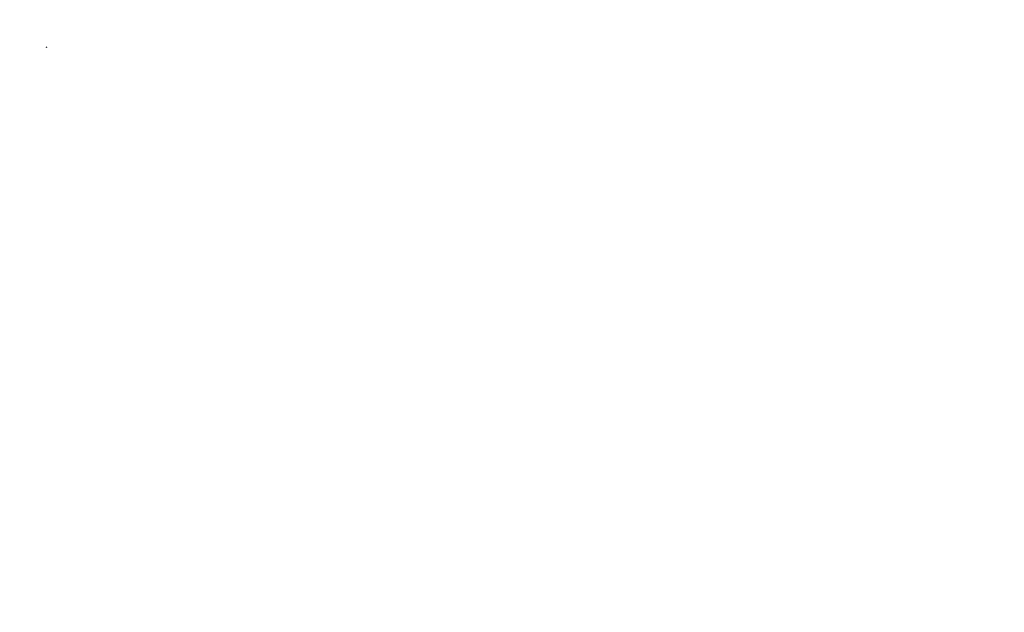
SolidWorks part; units mm, degrees
ref_plane "Front Plane" through (0, 0, 0) normal (0, 0, 1) x (1, 0, 0)
ref_plane "Top Plane" through (0, 0, 0) normal (0, 1, 0) x (1, 0, 0)
ref_plane "Right Plane" through (0, 0, 0) normal (1, 0, 0) x (0, 0, -1)
sketch "Sketch1" plane through (0, 0, 0) normal (0, 1, 0) x (1, 0, 0)
  line L0 (0, 10.9842) -> (0, -10.9842)
  arc A0 (0, -10.9842) -> (0, 10.9842) centre (0, 0) ccw
  dimension "D1" = 21.9685
revolve "Revolve-Sun" add sketch "Sketch1" angle 360 about L0
sketch "Sketch10" plane through (0, 0, 0) normal (0, 1, 0) x (1, 0, 0)
  line L0 (456.9844, 0.0394) -> (456.9844, -0.0394)
  circle A0 centre (0, 0) radius 456.9844 construction
  arc A1 (456.9844, -0.0394) -> (456.9844, 0.0394) centre (456.9844, 0) ccw
  dimension "D1" = 913.9687
  dimension "D2" = 0.0787
revolve "Revolve-Mercury" add sketch "Sketch10" angle 360 about L0
sketch "Sketch9" plane through (0, 0, 0) normal (0, 1, 0) x (1, 0, 0)
  line L0 (853.9235, 0.0955) -> (853.9235, -0.0955)
  circle A0 centre (0, 0) radius 853.9235 construction
  arc A1 (853.9235, -0.0955) -> (853.9235, 0.0955) centre (853.9235, 0) ccw
  dimension "D1" = 1707.847
  dimension "D2" = 0.191
revolve "Revolve-Venus" add sketch "Sketch9" angle 360 about L0
sketch "Sketch7" plane through (0, 0, 0) normal (0, 1, 0) x (1, 0, 0)
  line L0 (1180.5418, 0.1006) -> (1180.5418, -0.1006)
  circle A0 centre (0, 0) radius 1180.5418 construction
  arc A1 (1180.5418, -0.1006) -> (1180.5418, 0.1006) centre (1180.5418, 0) ccw
  dimension "D1" = 2361.0837
  dimension "D2" = 0.2011
revolve "Revolve-Earth" add sketch "Sketch7" angle 360 about L0
sketch "Sketch8" plane through (0, 0, 0) normal (0, 1, 0) x (1, 0, 0)
  line L0 (1183.5753, 0.0274) -> (1183.5753, -0.0274)
  circle A0 centre (1180.5418, 0) radius 3.0335 construction
  arc A1 (1183.5753, -0.0274) -> (1183.5753, 0.0274) centre (1183.5753, 0) ccw
  dimension "D1" = 6.0669
  dimension "D2" = 0.0548
revolve "Revolve-Moon" add sketch "Sketch8" angle 360 about L0
sketch "Sketch6" plane through (0, 0, 0) normal (0, 1, 0) x (1, 0, 0)
  line L0 (1798.762, 0.0534) -> (1798.762, -0.0534)
  circle A0 centre (0, 0) radius 1798.762 construction
  arc A1 (1798.762, -0.0534) -> (1798.762, 0.0534) centre (1798.762, 0) ccw
  dimension "D1" = 3597.5239
  dimension "D2" = 0.1069
revolve "Revolve-Mars" add sketch "Sketch6" angle 360 about L0
sketch "Sketch5" plane through (0, 0, 0) normal (0, 1, 0) x (1, 0, 0)
  line L0 (6143.8384, 1.0917) -> (6143.8384, -1.0917)
  circle A0 centre (0, 0) radius 6143.8384 construction
  arc A1 (6143.8384, -1.0917) -> (6143.8384, 1.0917) centre (6143.8384, 0) ccw
  dimension "D1" = 12287.6767
  dimension "D2" = 2.1835
revolve "Revolve-Jupiter" add sketch "Sketch5" angle 360 about L0
sketch "Sketch4" plane through (0, 0, 0) normal (0, 1, 0) x (1, 0, 0)
  line L0 (11311.9421, 0.9046) -> (11311.9421, -0.9046)
  circle A0 centre (0, 0) radius 11311.9421 construction
  arc A1 (11311.9421, -0.9046) -> (11311.9421, 0.9046) centre (11311.9421, 0) ccw
  dimension "D1" = 22623.8841
  dimension "D2" = 1.8092
revolve "Revolve-Saturn" add sketch "Sketch4" angle 360 about L0
sketch "Sketch3" plane through (0, 0, 0) normal (0, 1, 0) x (1, 0, 0)
  line L0 (22701.0722, 0.3988) -> (22701.0722, -0.3988)
  circle A0 centre (0, 0) radius 22701.0722 construction
  arc A1 (22701.0722, -0.3988) -> (22701.0722, 0.3988) centre (22701.0722, 0) ccw
  dimension "D1" = 45402.1444
  dimension "D2" = 0.7975
revolve "Revolve-Uranus" add sketch "Sketch3" angle 360 about L0
sketch "Sketch2" plane through (0, 0, 0) normal (0, 1, 0) x (1, 0, 0)
  line L0 (35538.41, 0.3875) -> (35538.41, -0.3875)
  circle A0 centre (0, 0) radius 35538.41 construction
  arc A1 (35538.41, -0.3875) -> (35538.41, 0.3875) centre (35538.41, 0) ccw
  dimension "D1" = 71076.82
  dimension "D2" = 0.775
revolve "Revolve-Neptune" add sketch "Sketch2" angle 360 about L0
sketch "Sketch-Orbits" plane through (0, 0, 0) normal (0, 1, 0) x (1, 0, 0)
  circle A0 centre (0, 0) radius 456.9844 construction
  circle A1 centre (0, 0) radius 456.9844 construction
  circle A2 centre (0, 0) radius 853.9235 construction
  circle A3 centre (0, 0) radius 1180.5418 construction
  circle A4 centre (0, 0) radius 1798.762 construction
  circle A5 centre (0, 0) radius 6143.8384 construction
  circle A6 centre (0, 0) radius 11311.9421 construction
  circle A7 centre (0, 0) radius 22701.0722 construction
  circle A8 centre (0, 0) radius 35538.41 construction
  circle A9 centre (0, 0) radius 853.9235 construction
  circle A10 centre (0, 0) radius 1180.5418 construction
  circle A11 centre (0, 0) radius 1798.762 construction
  circle A12 centre (0, 0) radius 6143.8384 construction
  circle A13 centre (0, 0) radius 11311.9421 construction
  circle A14 centre (0, 0) radius 22701.0722 construction
  circle A15 centre (0, 0) radius 35538.41 construction
  circle A16 centre (1180.5418, 0) radius 3.0335 construction
  circle A17 centre (1180.5418, 0) radius 3.0335 construction
sketch "Sketch-Axes" plane through (0, 0, 0) normal (1, 0, 0) x (0, 0, -1)
  line L0 (0, 10.426) -> (0, -49989.574) construction
  line L1 (-8.9818, 0) -> (49991.0182, 0) construction
sketch "Sketch-Day & Night for Mercury, Earth, & Neptune" plane through (0, 0, 0) normal (0, 1, 0) x (1, 0, 0)
  line L0 (0.2631, 10.9811) -> (456.9853, 0.0393)
  line L1 (0.2631, -10.9811) -> (456.9853, -0.0393)
  line L2 (456.9853, 0.0393) -> (456.9844, 0)
  line L3 (456.9844, 0) -> (456.9853, -0.0393)
  line L4 (0.1013, 10.9838) -> (1180.5428, 0.1006)
  line L5 (0.1013, -10.9838) -> (1180.5428, -0.1006)
  line L6 (1180.5428, 0.1006) -> (1180.5418, 0)
  line L7 (1180.5418, 0) -> (1180.5428, -0.1006)
  line L8 (0.0033, 10.9842) -> (35538.4101, 0.3875)
  line L9 (0.0033, -10.9842) -> (35538.4101, -0.3875)
  line L10 (35538.4101, 0.3875) -> (35538.41, 0)
  line L11 (35538.41, 0) -> (35538.4101, -0.3875)
  circle A0 centre (0, 0) radius 10.9842 construction
  circle A1 centre (456.9844, 0) radius 0.0394 construction
  circle A2 centre (456.9844, 0) radius 0.0394
  circle A5 centre (1180.5418, 0) radius 0.1006 construction
  circle A6 centre (1180.5418, 0) radius 0.1006
  circle A10 centre (35538.41, 0) radius 0.3875
  arc A11 (35538.41, -0.3875) -> (35538.41, 0.3875) centre (35538.41, 0) ccw construction
  circle A12 centre (0, 0) radius 10.9842
  dimension "D6" = 179.966
  dimension "D1" = 177.255
  dimension "D2" = 178.944
  dimension "D4" = 2.745
  dimension "D5" = 1.056
